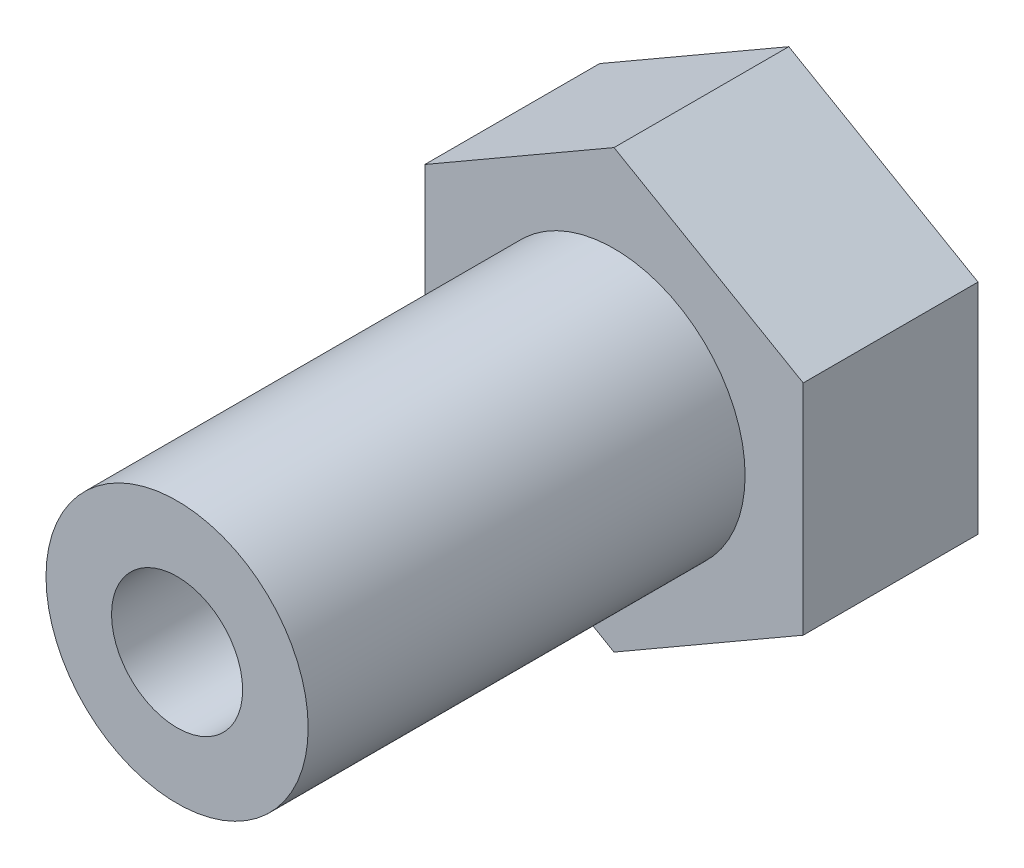
SolidWorks part; units mm, degrees
ref_plane "Plano frontal" through (0, 0, 0) normal (0, 0, 1) x (1, 0, 0)
ref_plane "Plano superior" through (0, 0, 0) normal (0, 1, 0) x (1, 0, 0)
ref_plane "Plano direito" through (0, 0, 0) normal (1, 0, 0) x (0, 0, -1)
sketch "Esboço1" plane through (0, 0, 0) normal (0, 0, 1) x (1, 0, 0)
  line L0 (-8.6603, 5) -> (-8.6603, -5)
  line L5 (8.6603, -5) -> (8.6603, 5)
  line L6 (8.6603, 5) -> (0, 10)
  line L7 (0, 10) -> (-8.6603, 5)
  line L8 (-8.6603, -5) -> (0, -10)
  line L9 (0, -10) -> (8.6603, -5)
  circle A1 centre (0, 0) radius 3
extrude "Ressalto-extrusão1" add sketch "Esboço1" along normal blind 8
sketch "Esboço2" plane through (0, 0, 0) normal (0, 0, -1) x (-1, 0, 0)
  circle A0 centre (0, 0) radius 5
  circle A1 centre (0, 0) radius 3
extrude "Ressalto-extrusão2" add sketch "Esboço2" along normal blind 1
sketch "Esboço3" plane through (0, 0, 8) normal (0, 0, 1) x (1, 0, 0)
  circle A0 centre (0, 0) radius 6
  circle A1 centre (0, 0) radius 3
extrude "Ressalto-extrusão3" add sketch "Esboço3" along normal blind 20
